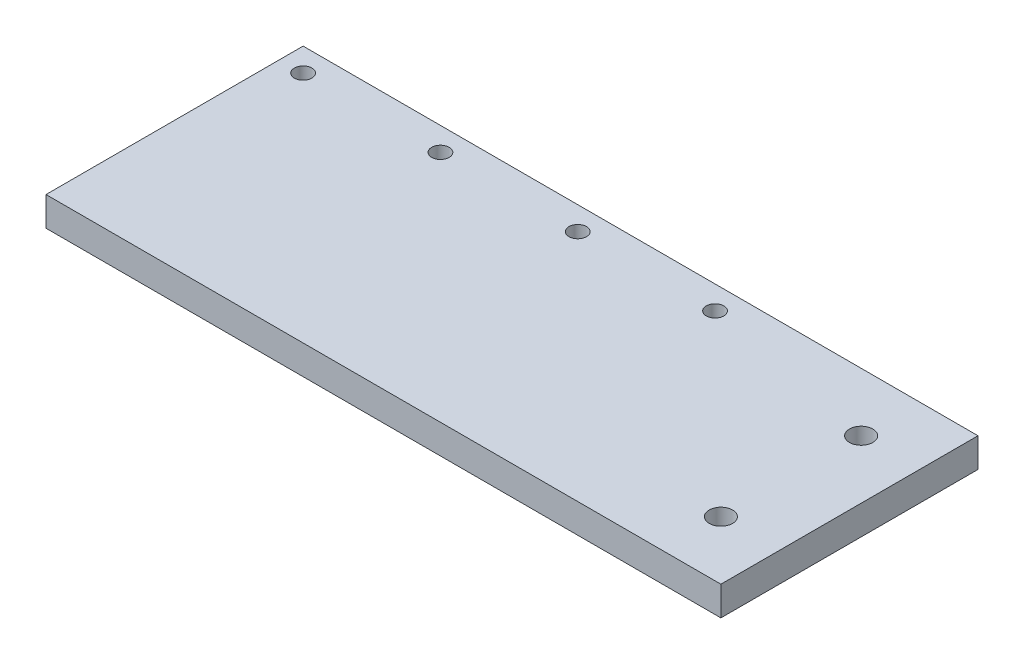
SolidWorks part; units mm, degrees
ref_plane "前视基准面" through (0, 0, 0) normal (0, 0, 1) x (1, 0, 0)
ref_plane "上视基准面" through (0, 0, 0) normal (0, 1, 0) x (1, 0, 0)
ref_plane "右视基准面" through (0, 0, 0) normal (1, 0, 0) x (0, 0, -1)
sketch "Sketch1" plane through (0, 0, 0) normal (0, 1, 0) x (1, 0, 0)
  line L1 (-47.75, 22) -> (47.75, 22)
  line L2 (-47.75, 22) -> (-47.75, -22)
  line L3 (-47.75, -22) -> (47.75, -22)
  line L4 (47.75, 22) -> (47.75, -22)
  line L5 (-47.75, 22) -> (47.75, -22) construction
  line L6 (-47.75, -22) -> (47.75, 22) construction
  point P0 (0, 0)
  dimension "D1" = 44
  dimension "95.5" = 95.5
extrude "Boss-Extrude1" add sketch "Sketch1" along normal blind 5
sketch "Sketch2" plane through (0, 5, 0) normal (0, 1, 0) x (1, 0, 0)
  line L0 (-47.75, 18) -> (47.75, 18) construction
  line L1 (-47.75, 22) -> (-47.75, -22) construction
  line L2 (47.75, -22) -> (47.75, 22) construction
  line L3 (47.75, 22) -> (-47.75, 22) construction
  circle A0 centre (-43.75, 18) radius 1.5
  circle A1 centre (-20.25, 18) radius 1.5
  circle A2 centre (3.25, 18) radius 1.5
  circle A3 centre (26.75, 18) radius 1.5
  dimension "D2" = 4
  dimension "D3" = 3
  dimension "D1" = 4
  dimension "D4" = 4
extrude "Cut-Extrude1" cut sketch "Sketch2" against normal through all
sketch "Sketch3" plane through (0, 5, 0) normal (0, 1, 0) x (1, 0, 0)
  line L0 (-47.75, -22) -> (47.75, -22) construction
  line L1 (47.75, 22) -> (67.75, 22)
  line L2 (47.75, 22) -> (47.75, -22)
  line L3 (47.75, -22) -> (67.75, -22)
  line L4 (67.75, 22) -> (67.75, -22)
  line L5 (57.75, 22) -> (57.75, -22) construction
  circle A0 centre (57.75, 12) radius 2
  circle A1 centre (57.75, -12) radius 2
  dimension "D2" = 4
  dimension "D3" = 4
  dimension "D4" = 10
  dimension "D5" = 10
  dimension "D1" = 20
extrude "Boss-Extrude2" add sketch "Sketch3" against normal blind 5
